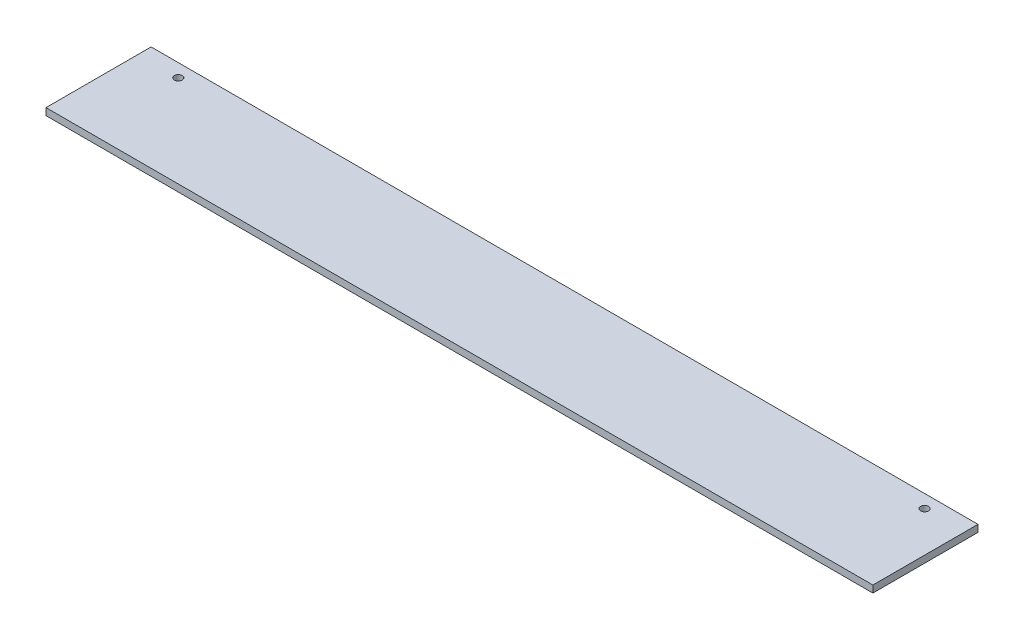
SolidWorks part; units mm, degrees
ref_plane "Спереди" through (0, 0, 0) normal (0, 0, 1) x (1, 0, 0)
ref_plane "Сверху" through (0, 0, 0) normal (0, 1, 0) x (1, 0, 0)
ref_plane "Справа" through (0, 0, 0) normal (1, 0, 0) x (0, 0, -1)
sketch "Эскиз1" plane through (0, 0, 0) normal (1, 0, 0) x (0, 0, -1)
  line L1 (-30, -2) -> (30, -2)
  line L2 (-30, -2) -> (-30, 2)
  line L3 (-30, 2) -> (30, 2)
  line L4 (30, -2) -> (30, 2)
  line L5 (-30, -2) -> (30, 2) construction
  line L6 (-30, 2) -> (30, -2) construction
  point P0 (0, 0)
  dimension "D1" = 4
  dimension "D2" = 60
extrude "Бобышка-Вытянуть1" add sketch "Эскиз1" along normal blind 472
sketch "Эскиз2" plane through (0, 2, 0) normal (0, 1, 0) x (1, 0, 0)
  line L0 (472, 30) -> (0, 30) construction
  line L1 (0, 30) -> (0, -30) construction
  line L2 (472, 30) -> (472, -30) construction
  circle A0 centre (23, 22.5) radius 2.25
  circle A1 centre (449, 22.5) radius 2.25
  dimension "D1" = 4.5
  dimension "D4" = 4.5
  dimension "D2" = 7.5
  dimension "D3" = 23
  dimension "D5" = 23
  dimension "D6" = 7.5
extrude "Вырез-Вытянуть1" cut sketch "Эскиз2" against normal through all
